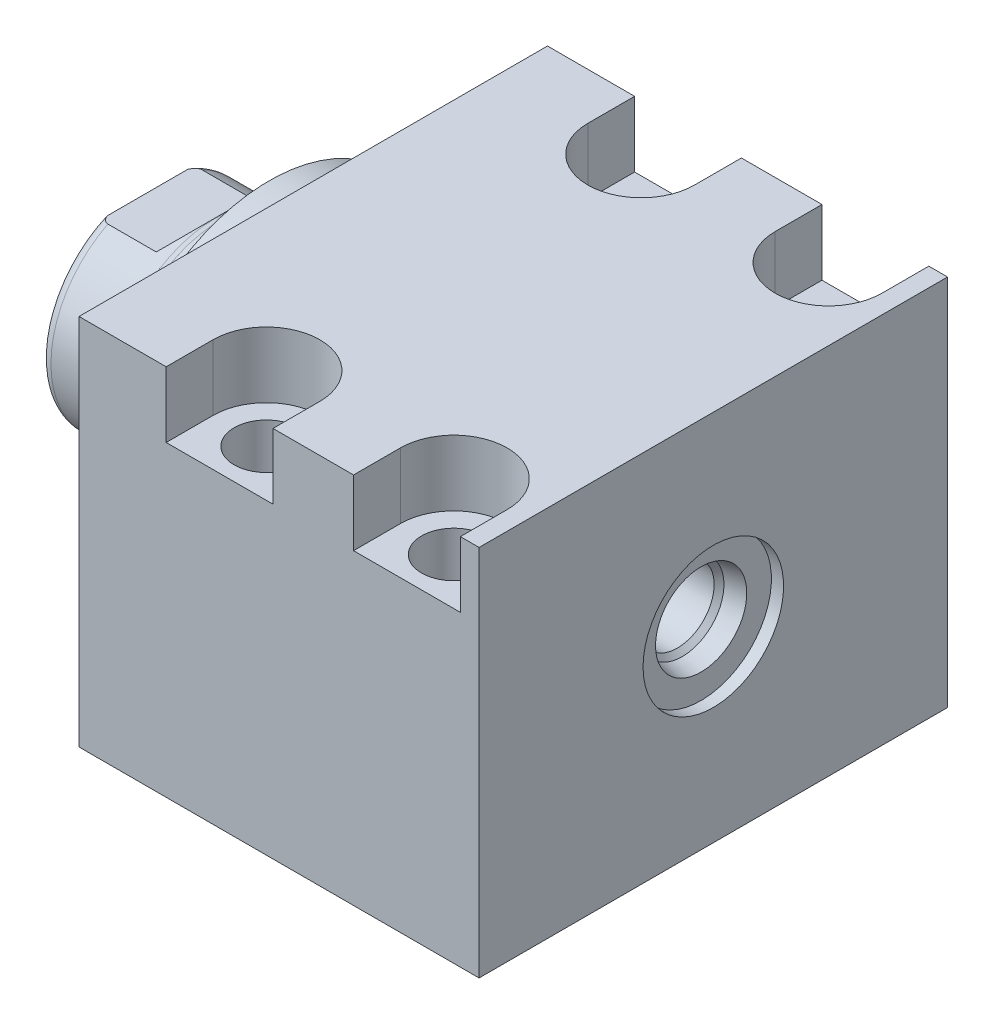
SolidWorks part; units mm, degrees
material "Alloy Steel"
ref_plane "Front Plane" through (0, 0, 0) normal (0, 0, 1) x (1, 0, 0)
ref_plane "Top Plane" through (0, 0, 0) normal (0, 1, 0) x (1, 0, 0)
ref_plane "Right Plane" through (0, 0, 0) normal (1, 0, 0) x (0, 0, -1)
ref_plane "Plane1" through (0, 0, 0) normal (1, 0, 0) x (0, 0, -1)
sketch "Sketch1" plane through (0, 0, 0) normal (1, 0, 0) x (0, 0, -1)
  line L0 (-31.75, 25.146) -> (31.75, 25.146)
  line L1 (31.75, 25.146) -> (31.75, -25.4)
  line L2 (31.75, -25.4) -> (-31.75, -25.4)
  line L3 (-31.75, -25.4) -> (-31.75, 25.146)
  line L4 (0, -24.4475) -> (0, 24.4475) construction
  dimension "D1" = 50.546
  dimension "D2" = 25.4
  dimension "D3" = 63.5
  dimension "D4" = 31.75
extrude "Extrude1" add sketch "Sketch1" along normal blind 54.229
sketch "Sketch5" plane through (0, 0, 0) normal (-1, 0, 0) x (0, 0, 1)
  circle A0 centre (0, 0) radius 22.225
  dimension "D1" = 44.45
extrude "Extrude2" add sketch "Sketch5" along normal blind 5.969
ref_plane "Plane5" through (0, 0, 0) normal (0, -1, 0) x (0, 0, 1)
sketch "Sketch6" plane through (0, 0, 0) normal (0, -1, 0) x (0, 0, 1)
  line L0 (0, 5.969) -> (-14.2875, 5.969)
  line L1 (-14.2875, 5.969) -> (-14.2875, 22.479)
  line L2 (-14.2875, 22.479) -> (0, 22.479)
  line L3 (0, 22.479) -> (0, 5.969)
  line L4 (0, -5.7546) -> (0, 21.1709) construction
  line L5 (22.225, 5.969) -> (-22.225, 5.969) construction
  line L6 (31.75, -54.229) -> (-31.75, -54.229) construction
  dimension "D1" = 76.708
  dimension "D2" = 28.575
revolve "Revolve1" add sketch "Sketch6" angle 360 about L4
ref_plane "Plane6" through (-18.5113, 3.2639, 0) normal (0, 0, 1) x (0, 1, 0)
sketch "S2D0001" plane through (-18.5113, 3.2639, 0) normal (0, 0, 1) x (0, 1, 0)
  line L0 (2.286, 1.9) -> (2.286, -14.6505)
  line L2 (3.4798, 3.9677) -> (-3.2639, 3.9677)
  line L3 (-3.2639, 3.9677) -> (-3.2639, -14.6505)
  line L4 (2.286, 1.9) -> (3.4798, 3.9677)
  line L5 (-3.2639, -18.5113) -> (-3.2639, 2.765) construction
  line L6 (11.0236, 3.9677) -> (-17.5514, 3.9677) construction
  line L7 (2.286, -14.6505) -> (-3.2639, -14.6505)
  dimension "D1" = 30
  dimension "D2" = 13.4874
  dimension "D3" = 11.0998
  dimension "D4" = 18.6182
revolve "Cut-Revolve4" cut sketch "S2D0001" angle 360 about L5
ref_plane "Plane7" through (0, 0, 0) normal (0, 1, 0) x (0, 0, -1)
sketch "Sketch8" plane through (0, 0, 0) normal (0, 1, 0) x (0, 0, -1)
  line L0 (-14.2875, 12.573) -> (-14.097, 13.335)
  line L1 (-14.097, 13.335) -> (-14.097, 21.463)
  line L2 (0, 12.6594) -> (0, 20.8178) construction
  line L3 (-14.2875, 12.573) -> (-14.2875, 22.479)
  line L4 (-13.7089, 22.479) -> (-14.2875, 22.479)
  line L5 (14.2875, 22.479) -> (-14.2875, 22.479) construction
  line L6 (-14.2875, 22.479) -> (-14.2875, 5.969) construction
  arc A0 (-13.7089, 22.479) -> (-14.097, 21.463) centre (-12.573, 21.463) ccw
  dimension "D2" = 1.524
  dimension "D1" = 28.194
  dimension "D3" = 1.016
  dimension "D4" = 0.762
  dimension "D5" = 9.144
revolve "Cut-Revolve5" cut sketch "Sketch8" angle 360 about L2
ref_plane "Plane11" through (0, 0, 0) normal (0, 0, -1) x (0, -1, 0)
sketch "Sketch12" plane through (0, 0, 0) normal (0, 0, -1) x (0, -1, 0)
  line L0 (12.573, 22.479) -> (12.573, 14.9098)
  line L1 (12.573, 14.9098) -> (14.097, 13.3858)
  line L2 (-12.573, 22.479) -> (-12.573, 14.9098)
  line L3 (-12.573, 14.9098) -> (-14.097, 13.3858)
  line L4 (12.573, 22.479) -> (14.097, 22.479)
  line L5 (0, 13.7262) -> (0, 20.767) construction
  line L6 (-14.097, 13.3858) -> (-14.097, 22.479)
  line L8 (14.097, 13.335) -> (14.097, 21.463) construction
  line L9 (14.097, 13.3858) -> (14.097, 22.479)
  line L10 (-12.573, 22.479) -> (-14.097, 22.479)
  line L12 (13.7089, 22.479) -> (-13.7089, 22.479) construction
  dimension "D1" = 25.146
  dimension "D2" = 7.5692
  dimension "D3" = 45
extrude "Cut-Extrude4" cut sketch "Sketch12" against normal mid plane 60.96
hole_wizard "Hole2" positions "Sketch17" profile "Sketch16" legacy
sketch "Sketch17" plane through (0, 25.146, 0) normal (0, 1, 0) x (-1, 0, 0)
  line L0 (0, 0) -> (-59.3363, 0) construction
  line L1 (0, -31.75) -> (0, 31.75) construction
  point P0 (-19.05, -25.4)
  point P9 (-19.05, 25.4)
  dimension "D1" = 50.8
  dimension "D2" = 19.05
sketch "Sketch16" plane through (19.05, 25.146, -25.4) normal (1, 0, 0) x (0, 0, 1)
  line L0 (0, 0) -> (0, 50.546)
  line L1 (0, 50.546) -> (4.3688, 50.546)
  line L2 (4.3688, 50.546) -> (4.3688, 0)
  line L3 (4.3688, 0) -> (0, 0)
  line L4 (0, 110) -> (0, -10) construction
  dimension "Diameter" = 8.7376
  dimension "Depth" = 50.546
pattern_linear "LPattern1" count 2 spacing 25.4 along (1, 0, 0) of "Hole2"
sketch "Sketch18" plane through (0, 25.146, 0) normal (0, 1, 0) x (1, 0, 0)
  line L0 (0, 0) -> (50.053, 0) construction
  line L2 (54.229, -31.75) -> (0, -31.75) construction
  line L4 (51.689, -31.75) -> (37.211, -31.75)
  line L5 (11.811, -25.4) -> (11.811, -31.75)
  line L6 (26.289, -25.4) -> (26.289, -31.75)
  line L7 (37.211, -25.4) -> (37.211, -31.75)
  line L8 (51.689, 25.4) -> (51.689, 31.75)
  line L9 (26.289, -31.75) -> (11.811, -31.75)
  line L12 (26.289, 31.75) -> (11.811, 31.75)
  line L14 (37.211, 25.4) -> (37.211, 31.75)
  line L15 (26.289, 25.4) -> (26.289, 31.75)
  line L16 (11.811, 25.4) -> (11.811, 31.75)
  line L17 (51.689, 31.75) -> (37.211, 31.75)
  line L18 (51.689, -25.4) -> (51.689, -31.75)
  arc A0 (26.289, -25.4) -> (11.811, -25.4) centre (19.05, -25.4) ccw
  arc A1 (51.689, -25.4) -> (37.211, -25.4) centre (44.45, -25.4) ccw
  arc A2 (51.689, 25.4) -> (37.211, 25.4) centre (44.45, 25.4) cw
  arc A3 (26.289, 25.4) -> (11.811, 25.4) centre (19.05, 25.4) cw
  dimension "D1" = 14.478
extrude "Cut-Extrude5" cut sketch "Sketch18" against normal blind 8.89
hole_wizard "Hole3" positions "Sketch20" profile "Sketch19" legacy
sketch "Sketch20" plane through (0, -25.4, 0) normal (0, -1, 0) x (1, 0, 0)
  line L0 (0, 31.75) -> (0, -31.75) construction
  point P0 (12.7, 0)
  dimension "D1" = 12.7
sketch "Sketch19" plane through (12.7, -25.4, 0) normal (1, 0, 0) x (0, 0, -1)
  line L0 (0, 0) -> (0, 10.4789)
  line L1 (0, 10.4789) -> (1.5875, 9.525)
  line L2 (1.5875, 9.525) -> (1.5875, 1.4478)
  line L3 (1.5875, 1.4478) -> (5.6705, 1.4478)
  line L4 (5.6705, 0) -> (0, 0)
  line L5 (0, -11.3109) -> (0, 121.1557) construction
  line L6 (0, 10.4789) -> (-1.5875, 9.525) construction
  line L7 (5.6705, 1.4478) -> (5.6705, 0)
  dimension "Depth" = 9.525
  dimension "Drill Angle" = 118
  dimension "Diameter" = 3.175
  dimension "C-Bore Diameter" = 11.3411
  dimension "C-Bore Depth" = 1.4478
hole_wizard "Hole4" positions "Sketch21" profile "Sketch22" legacy
sketch "Sketch21" plane through (0, -25.4, 0) normal (0, -1, 0) x (1, 0, 0)
  point P0 (38.1, 0)
  dimension "D1" = 25.4
sketch "Sketch22" plane through (38.1, -25.4, 0) normal (1, 0, 0) x (0, 0, -1)
  line L0 (0, 0) -> (0, 10.4789)
  line L1 (0, 10.4789) -> (1.5875, 9.525)
  line L2 (1.5875, 9.525) -> (1.5875, 1.4478)
  line L3 (1.5875, 1.4478) -> (5.6705, 1.4478)
  line L4 (5.6705, 0) -> (0, 0)
  line L5 (0, -11.3109) -> (0, 121.1557) construction
  line L6 (0, 10.4789) -> (-1.5875, 9.525) construction
  line L7 (5.6705, 1.4478) -> (5.6705, 0)
  dimension "Depth" = 9.525
  dimension "Drill Angle" = 118
  dimension "Diameter" = 3.175
  dimension "C-Bore Diameter" = 11.3411
  dimension "C-Bore Depth" = 1.4478
chamfer "Chamfer1" distance 0.635 angle 45 2 edges at (38.1, -23.9522, -1.5875) (12.7, -23.9522, -1.5875)
sketch "Sketch23" plane through (0, 0, 0) normal (0, 0, 1) x (1, 0, 0)
  line L0 (12.7, -23.9522) -> (12.7, -21.4272) construction
  line L1 (10.4775, -23.9522) -> (14.9225, -23.9522) construction
  line L2 (7.0294, -23.9522) -> (18.3705, -23.9522) construction
  line L3 (7.0294, -23.9522) -> (7.0294, -25.4) construction
  circle A0 centre (8.4772, -25.4) radius 1.4478
  dimension "D1" = 2.8956
revolve "Revolve2" add sketch "Sketch23" angle 360 about L0
pattern_linear "LPattern3" count 2 spacing 25.4 along (1, 0, 0) of bodies 128
sketch "Sketch24" plane through (0, 0, 0) normal (0, 0, 1) x (1, 0, 0)
  line L0 (0, 0) -> (74.772, 0) construction
  line L1 (54.229, 9.525) -> (52.578, 9.525)
  line L2 (54.229, 25.146) -> (54.229, -25.4) construction
  line L3 (52.578, 9.525) -> (52.578, 6.1849)
  line L4 (52.578, 6.1849) -> (50.0253, 5.6423)
  line L5 (50.0253, 5.6423) -> (49.3614, 4.9784)
  line L6 (49.3614, 4.9784) -> (37.973, 4.9784)
  line L7 (37.973, 4.9784) -> (37.973, 0)
  line L8 (37.973, 0) -> (54.229, 0)
  line L9 (54.229, 0) -> (54.229, 9.525)
  dimension "D1" = 1.651
  dimension "D2" = 19.05
  dimension "D3" = 9.9568
  dimension "D4" = 16.256
  dimension "D5" = 12
  dimension "D6" = 45
  dimension "D7" = 12.3698
  dimension "D8" = 2.5527
revolve "Cut-Revolve6" cut sketch "Sketch24" angle 360 about L0
